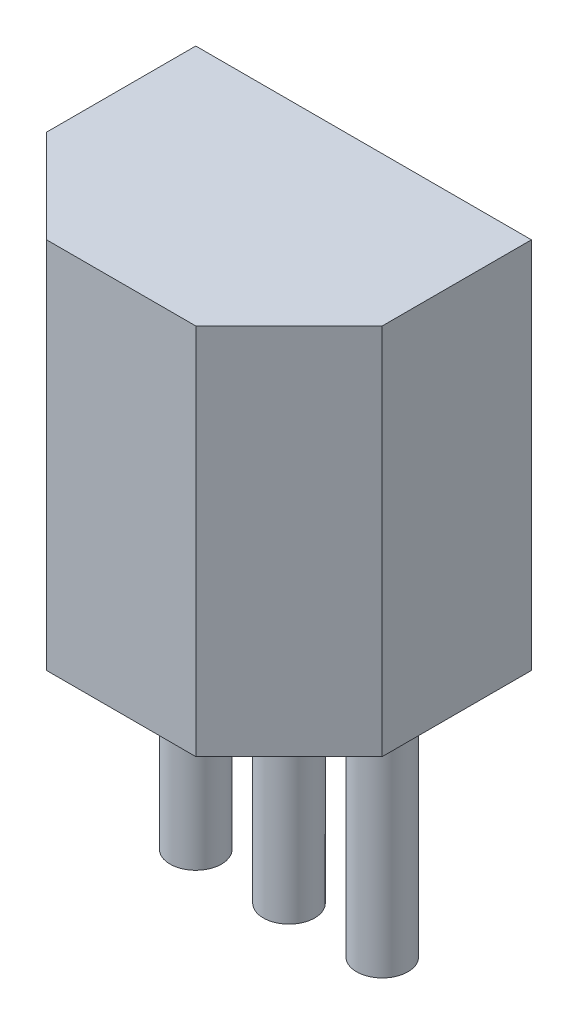
SolidWorks part; units mm, degrees
ref_plane "Front Plane" through (0, 0, 0) normal (0, 0, 1) x (1, 0, 0)
ref_plane "Top Plane" through (0, 0, 0) normal (0, 1, 0) x (1, 0, 0)
ref_plane "Right Plane" through (0, 0, 0) normal (1, 0, 0) x (0, 0, -1)
sketch "Sketch1" plane through (0, 0, 0) normal (0, 1, 0) x (1, 0, 0)
  line L0 (-1.016, -1.016) -> (0.254, -2.286)
  line L1 (-1.016, -1.016) -> (-1.016, 1.016)
  line L2 (-1.016, 1.016) -> (3.556, 1.016)
  line L3 (0.254, -2.286) -> (2.286, -2.286)
  line L4 (2.286, -2.286) -> (3.556, -1.016)
  line L5 (3.556, -1.016) -> (3.556, 1.016)
extrude "Boss-Extrude1" add sketch "Sketch1" along normal blind 5.08
sketch "Sketch2" plane through (0, 0, 0) normal (0, -1, 0) x (1, 0, 0)
  circle A0 centre (0, 0) radius 0.35
  circle A1 centre (1.27, 0) radius 0.35
  circle A2 centre (2.54, 0) radius 0.35
  dimension "D1" = 1.27
  dimension "D2" = 1.27
  dimension "D3" = 0.7
extrude "Boss-Extrude2" add sketch "Sketch2" along normal blind 3.38
ref_plane "Board Plane" through (0, -0.5, 0) normal (0, 1, 0) x (-1, 0, 0)
sketch "Component_Outline" plane through (0, -0.5, 0) normal (0, 1, 0) x (-1, 0, 0)
  line L0 (1.016, -1.016) -> (-3.556, -1.016)
  line L1 (-3.556, -1.016) -> (-3.556, 1.016)
  line L2 (-3.556, 1.016) -> (-2.286, 2.286)
  line L3 (-2.286, 2.286) -> (-0.254, 2.286)
  line L4 (-0.254, 2.286) -> (1.016, 1.016)
  line L5 (1.016, 1.016) -> (1.016, -1.016)
  point P4 (0, 0)
